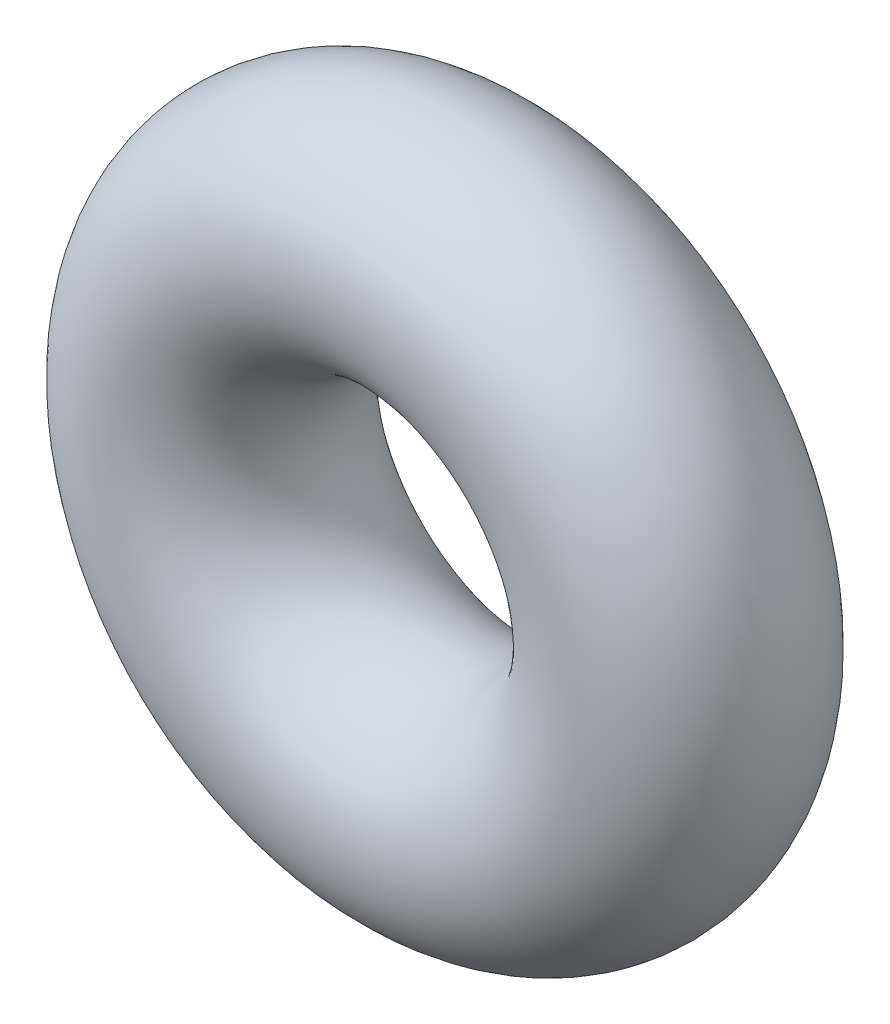
SolidWorks part; units mm, degrees
ref_plane "Front" through (0, 0, 0) normal (0, 0, 1) x (1, 0, 0)
ref_plane "Top" through (0, 0, 0) normal (0, 1, 0) x (1, 0, 0)
ref_plane "Right" through (0, 0, 0) normal (1, 0, 0) x (0, 0, -1)
sketch "Sketch1" plane through (0, 0, 0) normal (1, 0, 0) x (0, -1, 0)
  line L0 (0, -0.889) -> (0, 0.889) construction
  line L2 (-2.9337, 0) -> (2.9337, 0) construction
  line L3 (-0.889, 0) -> (0.889, 0) construction
  circle A0 centre (1.778, 0) radius 0.889
  point P9 (0.889, 0)
  point P10 (2.667, 0)
  point P13 (1.778, 0.889)
  point P14 (1.778, -0.889)
  dimension "Width" = 1.778
  dimension "ID" = 1.778
revolve "Revolve1" add sketch "Sketch1" angle 360 about L0
